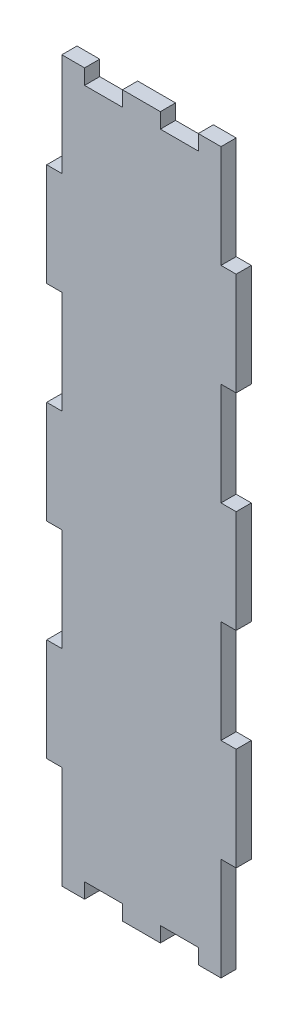
SolidWorks part; units mm, degrees
ref_plane "Front Plane" through (0, 0, 0) normal (0, 0, 1) x (1, 0, 0)
ref_plane "Top Plane" through (0, 0, 0) normal (0, 1, 0) x (1, 0, 0)
ref_plane "Right Plane" through (0, 0, 0) normal (1, 0, 0) x (0, 0, -1)
sketch "Buitenafmeting Rechthoek" plane through (0, 0, 0) normal (0, 0, 1) x (1, 0, 0)
  line L1 (0, 0) -> (50, 0)
  line L2 (0, 0) -> (0, 190)
  line L3 (0, 190) -> (50, 190)
  line L4 (50, 0) -> (50, 190)
  dimension "D1" = 50
  dimension "D2" = 190
extrude "Plaat" add sketch "Buitenafmeting Rechthoek" against normal blind 4
sketch "Tand Hor" plane through (0, 0, 0) normal (0, 0, 1) x (1, 0, 0)
  line L1 (50, 190) -> (0, 190) construction
  line L2 (10, 190) -> (20, 190)
  line L3 (10, 190) -> (10, 186)
  line L4 (10, 186) -> (20, 186)
  line L6 (20, 190) -> (20, 186)
  dimension "D1" = 4
  dimension "D2" = 10
  dimension "D3" = 10
extrude "Tand Boven" cut sketch "Tand Hor" against normal through all
pattern_linear "Tanden Patroon Boven" count 2 spacing 20 along (1, 0, 0) of "Tand Boven"
sketch "Tand Ver" plane through (0, 0, 0) normal (0, 0, 1) x (1, 0, 0)
  line L0 (0, 190) -> (0, 0) construction
  line L1 (0, 190) -> (4, 190)
  line L2 (0, 190) -> (0, 162.8571)
  line L3 (0, 162.8571) -> (4, 162.8571)
  line L4 (4, 190) -> (4, 162.8571)
  dimension "D1" = 4
  dimension "D2" = 27.1429
  dimension "D3" = 190
extrude "Tand Links" cut sketch "Tand Ver" against normal through all
pattern_linear "Tanden Patroon Links" count 4 spacing 54.2857 along (0, -1, 0) of "Tand Links"
sketch "Tand O" plane through (0, 0, 0) normal (0, 0, 1) x (1, 0, 0)
  line L0 (4, 0) -> (50, 0) construction
  line L1 (10, 0) -> (20, 0)
  line L2 (10, 0) -> (10, 4)
  line L3 (10, 4) -> (20, 4)
  line L4 (20, 0) -> (20, 4)
  dimension "D1" = 4
  dimension "D2" = 10
  dimension "D3" = 10
extrude "Tand Onder" cut sketch "Tand O" against normal through all
pattern_linear "Tanden Patroon Onder" count 2 spacing 20 along (1, 0, 0) of "Tand Onder"
sketch "Tand R" plane through (0, 0, 0) normal (0, 0, 1) x (1, 0, 0)
  line L0 (50, 0) -> (50, 190) construction
  line L1 (50, 190) -> (46, 190)
  line L2 (50, 190) -> (50, 162.8571)
  line L3 (50, 162.8571) -> (46, 162.8571)
  line L4 (46, 190) -> (46, 162.8571)
  dimension "D1" = 4
  dimension "D2" = 27.1429
  dimension "D3" = 190
extrude "Tand Rechts" cut sketch "Tand R" against normal through all
pattern_linear "Tanden Patroon Rechts" count 4 spacing 54.2857 along (0, -1, 0) of "Tand Rechts"
equation "\"D1@Buitenafmeting Rechthoek\"= \"Lengte\""
equation "\"D2@Buitenafmeting Rechthoek\" = \"Hoogte\""
equation "\"D1@Plaat\" = \"Dikte\""
equation "\"D3@Tanden Patroon Boven\" = \"LengteHorTand\" * 2"
equation "\"D1@Tanden Patroon Boven\" = \"nPatroonHor\""
equation "\"LengteHorTand\"= \"Lengte\" / \"nHor\"'Spatie tussen verschillende tanden in de lengte"
equation "\"nPatroonHor\"= ( \"nHor\" + 1 ) / 2 - \"GrensHor\"'Aantal kopies van tanden in de lengte"
equation "\"D1@Tand Hor\" = \"Dikte\""
equation "\"D2@Tand Hor\" = \"LengteHorTand\""
equation "\"D1@Tand Ver\" = \"Dikte\""
equation "\"LengteVertTand\"= \"Hoogte\" / \"nVert\"'Spatie tussen verschillende tanden in de hoogte"
equation "\"nPatroonVert\"= ( \"nVert\" + 1 ) / 2 - \"GrensVert\"'Aantal kopies van tanden in de hoogte"
equation "\"D2@Tand Ver\"=\"LengteVertTand\""
equation "\"D3@Tanden Patroon Links\"=\"LengteVertTand\"*2"
equation "\"D3@Tanden Patroon Rechts\"=\"LengteVertTand\"*2"
equation "\"D1@Tanden Patroon Rechts\"=\"nPatroonVert\""
equation "\"D3@Tanden Patroon Onder\"=\"LengteHorTand\"*2"
equation "\"D1@Tanden Patroon Onder\"=\"nPatroonHor\""
equation "\"D1@Tanden Patroon Links\"=\"nPatroonVert\""
equation "\"D3@Tand Ver\"=\"Hoogte\"-\"GrensVert\"*\"LengteVertTand\""
equation "\"D2@Tand R\" = \"LengteVertTand\""
equation "\"D3@Tand R\" = \"Hoogte\" - \"GrensVert\" * \"LengteVertTand\""
equation "\"D2@Tand O\"=\"LengteHorTand\""
equation "\"D3@Tand Hor\"=\"GrensHor\"*\"LengteHorTand\""
equation "\"D3@Tand O\"=\"GrensHor\"*\"LengteHorTand\""
equation "\"Tand Boven\"= IIF ( \"plaatsTandenBoven\" , \"unsuppressed\" , \"suppressed\" )"
equation "\"Tanden Patroon Boven\"= IIF ( \"plaatsTandenBoven\" , \"unsuppressed\" , \"suppressed\" )"
equation "\"Tand Links\"= IIF ( \"plaatsTandenLinks\" , \"unsuppressed\" , \"suppressed\" )"
equation "\"Tanden Patroon Links\"= IIF ( \"plaatsTandenLinks\" , \"unsuppressed\" , \"suppressed\" )"
equation "\"Tand Onder\"= IIF ( \"plaatsTandenOnder\" , \"unsuppressed\" , \"suppressed\" )"
equation "\"Tanden Patroon Onder\"= IIF ( \"plaatsTandenOnder\" , \"unsuppressed\" , \"suppressed\" )"
equation "\"Tand Rechts\"= IIF ( \"plaatsTandenRechts\" , \"unsuppressed\" , \"suppressed\" )"
equation "\"Tanden Patroon Rechts\"= IIF ( \"plaatsTandenRechts\" , \"unsuppressed\" , \"suppressed\" )"
equation "\"D1@Tand O\"=\"Dikte\""
equation "\"D1@Tand R\"=\"Dikte\""
